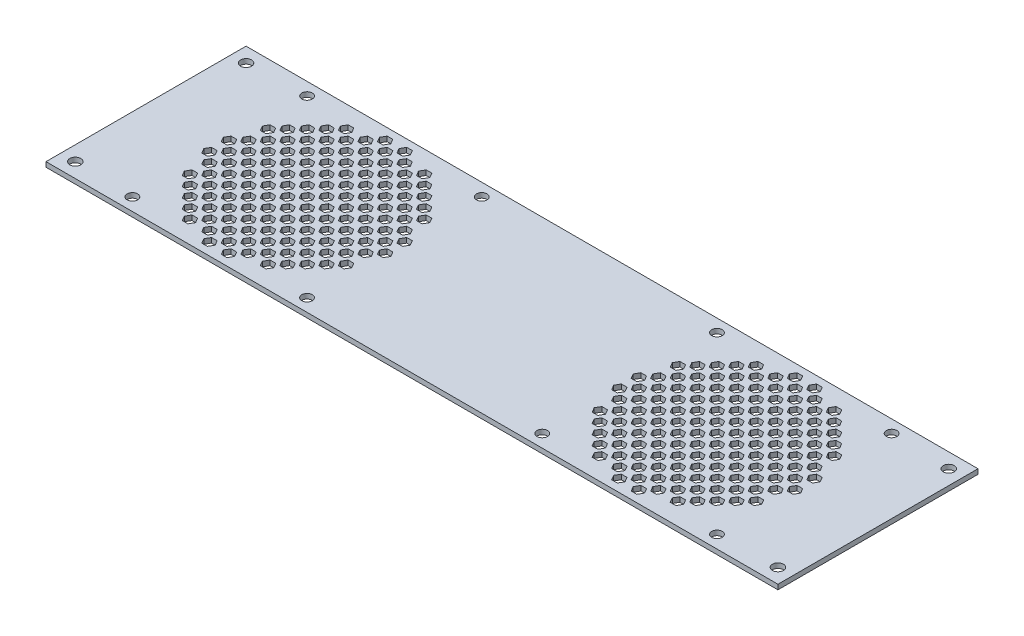
SolidWorks part; units mm, degrees
ref_plane "Front Plane" through (0, 0, 0) normal (0, 0, 1) x (1, 0, 0)
ref_plane "Top Plane" through (0, 0, 0) normal (0, 1, 0) x (1, 0, 0)
ref_plane "Right Plane" through (0, 0, 0) normal (1, 0, 0) x (0, 0, -1)
sketch "Sketch1" plane through (0, 0, 0) normal (0, 1, 0) x (1, 0, 0)
  line L1 (0, 0) -> (300, 0)
  line L2 (0, 0) -> (0, 82)
  line L3 (0, 82) -> (300, 82)
  line L4 (300, 0) -> (300, 82)
  dimension "D1" = 82
  dimension "D2" = 300
extrude "Boss-Extrude1" add sketch "Sketch1" along normal blind 2
hole_wizard "M4 Clearance Hole1" positions "Sketch2" profile "Sketch3" hole size "M4" standard "DIN" end condition up to next
sketch "Sketch2" plane through (0, 0, 0) normal (0, -1, 0) x (-1, 0, 0)
  line L0 (-300, 82) -> (0, 82) construction
  line L1 (-300, 0) -> (-300, 82) construction
  line L2 (0, 0) -> (-300, 0) construction
  line L3 (0, 82) -> (0, 0) construction
  point P0 (-294, 76)
  point P2 (-294, 6)
  point P4 (-6, 6)
  point P6 (-6, 76)
  dimension "D1" = 6
  dimension "D2" = 6
  dimension "D3" = 6
  dimension "D4" = 6
sketch "Sketch3" plane through (294, 0, -76) normal (1, 0, 0) x (0, 0, -1)
  line L0 (0, 0) -> (0, 2)
  line L1 (0, 2) -> (2.25, 2)
  line L2 (2.25, 2) -> (2.25, 0)
  line L5 (2.25, 0) -> (0, 0)
  line L11 (0, -6.35) -> (0, 107.95) construction
  dimension "Thru Hole Dia." = 4.5
  dimension "Thru Hole Depth" = 2
sketch "Sketch5" plane through (0, 0, 0) normal (0, -1, 0) x (1, 0, 0)
  line L0 (0, -82) -> (0, 0) construction
  line L1 (67.1547, -39) -> (64.8453, -39)
  line L2 (64.8453, -39) -> (63.6906, -41)
  line L3 (63.6906, -41) -> (64.8453, -43)
  line L4 (64.8453, -43) -> (67.1547, -43)
  line L5 (67.1547, -43) -> (68.3094, -41)
  line L6 (68.3094, -41) -> (67.1547, -39)
  line L7 (75.1547, -39) -> (72.8453, -39)
  line L8 (72.8453, -39) -> (71.6906, -41)
  line L9 (71.6906, -41) -> (72.8453, -43)
  line L10 (72.8453, -43) -> (75.1547, -43)
  line L11 (75.1547, -43) -> (76.3094, -41)
  line L12 (76.3094, -41) -> (75.1547, -39)
  line L13 (83.1547, -39) -> (80.8453, -39)
  line L14 (80.8453, -39) -> (79.6906, -41)
  line L15 (79.6906, -41) -> (80.8453, -43)
  line L16 (80.8453, -43) -> (83.1547, -43)
  line L17 (83.1547, -43) -> (84.3094, -41)
  line L18 (84.3094, -41) -> (83.1547, -39)
  line L19 (91.1547, -39) -> (88.8453, -39)
  line L20 (88.8453, -39) -> (87.6906, -41)
  line L21 (87.6906, -41) -> (88.8453, -43)
  line L22 (88.8453, -43) -> (91.1547, -43)
  line L23 (91.1547, -43) -> (92.3094, -41)
  line L24 (92.3094, -41) -> (91.1547, -39)
  line L25 (99.1547, -39) -> (96.8453, -39)
  line L26 (96.8453, -39) -> (95.6906, -41)
  line L27 (95.6906, -41) -> (96.8453, -43)
  line L28 (96.8453, -43) -> (99.1547, -43)
  line L29 (99.1547, -43) -> (100.3094, -41)
  line L30 (100.3094, -41) -> (99.1547, -39)
  line L31 (75.1547, -31) -> (72.8453, -31)
  line L32 (72.8453, -31) -> (71.6906, -33)
  line L33 (71.6906, -33) -> (72.8453, -35)
  line L34 (72.8453, -35) -> (75.1547, -35)
  line L35 (75.1547, -35) -> (76.3094, -33)
  line L36 (76.3094, -33) -> (75.1547, -31)
  line L37 (83.1547, -31) -> (80.8453, -31)
  line L38 (80.8453, -31) -> (79.6906, -33)
  line L39 (79.6906, -33) -> (80.8453, -35)
  line L40 (80.8453, -35) -> (83.1547, -35)
  line L41 (83.1547, -35) -> (84.3094, -33)
  line L42 (84.3094, -33) -> (83.1547, -31)
  line L43 (91.1547, -31) -> (88.8453, -31)
  line L44 (88.8453, -31) -> (87.6906, -33)
  line L45 (87.6906, -33) -> (88.8453, -35)
  line L46 (88.8453, -35) -> (91.1547, -35)
  line L47 (91.1547, -35) -> (92.3094, -33)
  line L48 (92.3094, -33) -> (91.1547, -31)
  line L49 (99.1547, -31) -> (96.8453, -31)
  line L50 (96.8453, -31) -> (95.6906, -33)
  line L51 (95.6906, -33) -> (96.8453, -35)
  line L52 (96.8453, -35) -> (99.1547, -35)
  line L53 (99.1547, -35) -> (100.3094, -33)
  line L54 (100.3094, -33) -> (99.1547, -31)
  line L55 (75.1547, -23) -> (72.8453, -23)
  line L56 (72.8453, -23) -> (71.6906, -25)
  line L57 (71.6906, -25) -> (72.8453, -27)
  line L58 (72.8453, -27) -> (75.1547, -27)
  line L59 (75.1547, -27) -> (76.3094, -25)
  line L60 (76.3094, -25) -> (75.1547, -23)
  line L61 (83.1547, -23) -> (80.8453, -23)
  line L62 (80.8453, -23) -> (79.6906, -25)
  line L63 (79.6906, -25) -> (80.8453, -27)
  line L64 (80.8453, -27) -> (83.1547, -27)
  line L65 (83.1547, -27) -> (84.3094, -25)
  line L66 (84.3094, -25) -> (83.1547, -23)
  line L67 (91.1547, -23) -> (88.8453, -23)
  line L68 (88.8453, -23) -> (87.6906, -25)
  line L69 (87.6906, -25) -> (88.8453, -27)
  line L70 (88.8453, -27) -> (91.1547, -27)
  line L71 (91.1547, -27) -> (92.3094, -25)
  line L72 (92.3094, -25) -> (91.1547, -23)
  line L73 (99.1547, -23) -> (96.8453, -23)
  line L74 (96.8453, -23) -> (95.6906, -25)
  line L75 (95.6906, -25) -> (96.8453, -27)
  line L76 (96.8453, -27) -> (99.1547, -27)
  line L77 (99.1547, -27) -> (100.3094, -25)
  line L78 (100.3094, -25) -> (99.1547, -23)
  line L79 (75.1547, -15) -> (72.8453, -15)
  line L80 (72.8453, -15) -> (71.6906, -17)
  line L81 (71.6906, -17) -> (72.8453, -19)
  line L82 (72.8453, -19) -> (75.1547, -19)
  line L83 (75.1547, -19) -> (76.3094, -17)
  line L84 (76.3094, -17) -> (75.1547, -15)
  line L85 (83.1547, -15) -> (80.8453, -15)
  line L86 (80.8453, -15) -> (79.6906, -17)
  line L87 (79.6906, -17) -> (80.8453, -19)
  line L88 (80.8453, -19) -> (83.1547, -19)
  line L89 (83.1547, -19) -> (84.3094, -17)
  line L90 (84.3094, -17) -> (83.1547, -15)
  line L91 (91.1547, -15) -> (88.8453, -15)
  line L92 (88.8453, -15) -> (87.6906, -17)
  line L93 (87.6906, -17) -> (88.8453, -19)
  line L94 (88.8453, -19) -> (91.1547, -19)
  line L95 (91.1547, -19) -> (92.3094, -17)
  line L96 (92.3094, -17) -> (91.1547, -15)
  line L103 (75.1547, -7) -> (72.8453, -7)
  line L104 (72.8453, -7) -> (71.6906, -9)
  line L105 (71.6906, -9) -> (72.8453, -11)
  line L106 (72.8453, -11) -> (75.1547, -11)
  line L107 (75.1547, -11) -> (76.3094, -9)
  line L108 (76.3094, -9) -> (75.1547, -7)
  line L109 (83.1547, -7) -> (80.8453, -7)
  line L110 (80.8453, -7) -> (79.6906, -9)
  line L111 (79.6906, -9) -> (80.8453, -11)
  line L112 (80.8453, -11) -> (83.1547, -11)
  line L113 (83.1547, -11) -> (84.3094, -9)
  line L114 (84.3094, -9) -> (83.1547, -7)
  line L127 (67.1547, -31) -> (64.8453, -31)
  line L128 (64.8453, -31) -> (63.6906, -33)
  line L129 (63.6906, -33) -> (64.8453, -35)
  line L130 (64.8453, -35) -> (67.1547, -35)
  line L131 (67.1547, -35) -> (68.3094, -33)
  line L132 (68.3094, -33) -> (67.1547, -31)
  line L133 (67.1547, -23) -> (64.8453, -23)
  line L134 (64.8453, -23) -> (63.6906, -25)
  line L135 (63.6906, -25) -> (64.8453, -27)
  line L136 (64.8453, -27) -> (67.1547, -27)
  line L137 (67.1547, -27) -> (68.3094, -25)
  line L138 (68.3094, -25) -> (67.1547, -23)
  line L139 (67.1547, -15) -> (64.8453, -15)
  line L140 (64.8453, -15) -> (63.6906, -17)
  line L141 (63.6906, -17) -> (64.8453, -19)
  line L142 (64.8453, -19) -> (67.1547, -19)
  line L143 (67.1547, -19) -> (68.3094, -17)
  line L144 (68.3094, -17) -> (67.1547, -15)
  line L145 (67.1547, -7) -> (64.8453, -7)
  line L146 (64.8453, -7) -> (63.6906, -9)
  line L147 (63.6906, -9) -> (64.8453, -11)
  line L148 (64.8453, -11) -> (67.1547, -11)
  line L149 (67.1547, -11) -> (68.3094, -9)
  line L150 (68.3094, -9) -> (67.1547, -7)
  line L151 (91.1547, -7) -> (88.8453, -7) [skipped]
  line L152 (88.8453, -7) -> (87.6906, -9) [skipped]
  line L153 (87.6906, -9) -> (88.8453, -11) [skipped]
  line L154 (88.8453, -11) -> (91.1547, -11) [skipped]
  line L155 (91.1547, -11) -> (92.3094, -9) [skipped]
  line L156 (92.3094, -9) -> (91.1547, -7) [skipped]
  line L157 (99.1547, -7) -> (96.8453, -7) [skipped]
  line L158 (96.8453, -7) -> (95.6906, -9) [skipped]
  line L159 (95.6906, -9) -> (96.8453, -11) [skipped]
  line L160 (96.8453, -11) -> (99.1547, -11) [skipped]
  line L161 (99.1547, -11) -> (100.3094, -9) [skipped]
  line L162 (100.3094, -9) -> (99.1547, -7) [skipped]
  line L163 (99.1547, -15) -> (96.8453, -15) [skipped]
  line L164 (96.8453, -15) -> (95.6906, -17) [skipped]
  line L165 (95.6906, -17) -> (96.8453, -19) [skipped]
  line L166 (96.8453, -19) -> (99.1547, -19) [skipped]
  line L167 (99.1547, -19) -> (100.3094, -17) [skipped]
  line L168 (100.3094, -17) -> (99.1547, -15) [skipped]
  circle A0 centre (66, -41) radius 2 construction
  point P12 (0, -41)
  dimension "D2" = 4
  dimension "D1" = 66
  dimension "D5" = 8
  dimension "D6" = 8
  dimension "D3" = 5
  dimension "D4" = 5
extrude "Cut-Extrude1" cut sketch "Sketch5" against normal up to next (2 mm away)
sketch "Sketch6" plane through (0, 0, 0) normal (0, -1, 0) x (1, 0, 0)
  line L0 (67.1547, -39) -> (64.8453, -39) construction
  line L1 (72.3094, -37) -> (71.1547, -35)
  line L2 (71.1547, -35) -> (68.8453, -35)
  line L3 (68.8453, -35) -> (67.6906, -37)
  line L4 (67.6906, -37) -> (68.8453, -39)
  line L5 (68.8453, -39) -> (71.1547, -39)
  line L6 (71.1547, -39) -> (72.3094, -37)
  line L7 (64.8453, -43) -> (67.1547, -43) construction
  line L9 (80.3094, -37) -> (79.1547, -35)
  line L10 (79.1547, -35) -> (76.8453, -35)
  line L11 (76.8453, -35) -> (75.6906, -37)
  line L12 (75.6906, -37) -> (76.8453, -39)
  line L13 (76.8453, -39) -> (79.1547, -39)
  line L14 (79.1547, -39) -> (80.3094, -37)
  line L15 (88.3094, -37) -> (87.1547, -35)
  line L16 (87.1547, -35) -> (84.8453, -35)
  line L17 (84.8453, -35) -> (83.6906, -37)
  line L18 (83.6906, -37) -> (84.8453, -39)
  line L19 (84.8453, -39) -> (87.1547, -39)
  line L20 (87.1547, -39) -> (88.3094, -37)
  line L21 (96.3094, -37) -> (95.1547, -35)
  line L22 (95.1547, -35) -> (92.8453, -35)
  line L23 (92.8453, -35) -> (91.6906, -37)
  line L24 (91.6906, -37) -> (92.8453, -39)
  line L25 (92.8453, -39) -> (95.1547, -39)
  line L26 (95.1547, -39) -> (96.3094, -37)
  line L27 (104.3094, -37) -> (103.1547, -35)
  line L28 (103.1547, -35) -> (100.8453, -35)
  line L29 (100.8453, -35) -> (99.6906, -37)
  line L30 (99.6906, -37) -> (100.8453, -39)
  line L31 (100.8453, -39) -> (103.1547, -39)
  line L32 (103.1547, -39) -> (104.3094, -37)
  line L33 (80.3094, -29) -> (79.1547, -27)
  line L34 (79.1547, -27) -> (76.8453, -27)
  line L35 (76.8453, -27) -> (75.6906, -29)
  line L36 (75.6906, -29) -> (76.8453, -31)
  line L37 (76.8453, -31) -> (79.1547, -31)
  line L38 (79.1547, -31) -> (80.3094, -29)
  line L39 (88.3094, -29) -> (87.1547, -27)
  line L40 (87.1547, -27) -> (84.8453, -27)
  line L41 (84.8453, -27) -> (83.6906, -29)
  line L42 (83.6906, -29) -> (84.8453, -31)
  line L43 (84.8453, -31) -> (87.1547, -31)
  line L44 (87.1547, -31) -> (88.3094, -29)
  line L45 (96.3094, -29) -> (95.1547, -27)
  line L46 (95.1547, -27) -> (92.8453, -27)
  line L47 (92.8453, -27) -> (91.6906, -29)
  line L48 (91.6906, -29) -> (92.8453, -31)
  line L49 (92.8453, -31) -> (95.1547, -31)
  line L50 (95.1547, -31) -> (96.3094, -29)
  line L57 (80.3094, -21) -> (79.1547, -19)
  line L58 (79.1547, -19) -> (76.8453, -19)
  line L59 (76.8453, -19) -> (75.6906, -21)
  line L60 (75.6906, -21) -> (76.8453, -23)
  line L61 (76.8453, -23) -> (79.1547, -23)
  line L62 (79.1547, -23) -> (80.3094, -21)
  line L63 (88.3094, -21) -> (87.1547, -19)
  line L64 (87.1547, -19) -> (84.8453, -19)
  line L65 (84.8453, -19) -> (83.6906, -21)
  line L66 (83.6906, -21) -> (84.8453, -23)
  line L67 (84.8453, -23) -> (87.1547, -23)
  line L68 (87.1547, -23) -> (88.3094, -21)
  line L69 (96.3094, -21) -> (95.1547, -19)
  line L70 (95.1547, -19) -> (92.8453, -19)
  line L71 (92.8453, -19) -> (91.6906, -21)
  line L72 (91.6906, -21) -> (92.8453, -23)
  line L73 (92.8453, -23) -> (95.1547, -23)
  line L74 (95.1547, -23) -> (96.3094, -21)
  line L81 (80.3094, -13) -> (79.1547, -11)
  line L82 (79.1547, -11) -> (76.8453, -11)
  line L83 (76.8453, -11) -> (75.6906, -13)
  line L84 (75.6906, -13) -> (76.8453, -15)
  line L85 (76.8453, -15) -> (79.1547, -15)
  line L86 (79.1547, -15) -> (80.3094, -13)
  line L87 (88.3094, -13) -> (87.1547, -11)
  line L88 (87.1547, -11) -> (84.8453, -11)
  line L89 (84.8453, -11) -> (83.6906, -13)
  line L90 (83.6906, -13) -> (84.8453, -15)
  line L91 (84.8453, -15) -> (87.1547, -15)
  line L92 (87.1547, -15) -> (88.3094, -13)
  line L129 (72.3094, -29) -> (71.1547, -27)
  line L130 (71.1547, -27) -> (68.8453, -27)
  line L131 (68.8453, -27) -> (67.6906, -29)
  line L132 (67.6906, -29) -> (68.8453, -31)
  line L133 (68.8453, -31) -> (71.1547, -31)
  line L134 (71.1547, -31) -> (72.3094, -29)
  line L135 (72.3094, -21) -> (71.1547, -19)
  line L136 (71.1547, -19) -> (68.8453, -19)
  line L137 (68.8453, -19) -> (67.6906, -21)
  line L138 (67.6906, -21) -> (68.8453, -23)
  line L139 (68.8453, -23) -> (71.1547, -23)
  line L140 (71.1547, -23) -> (72.3094, -21)
  line L141 (72.3094, -13) -> (71.1547, -11)
  line L142 (71.1547, -11) -> (68.8453, -11)
  line L143 (68.8453, -11) -> (67.6906, -13)
  line L144 (67.6906, -13) -> (68.8453, -15)
  line L145 (68.8453, -15) -> (71.1547, -15)
  line L146 (71.1547, -15) -> (72.3094, -13)
  line L147 (72.3094, -5) -> (71.1547, -3)
  line L148 (71.1547, -3) -> (68.8453, -3)
  line L149 (68.8453, -3) -> (67.6906, -5)
  line L150 (67.6906, -5) -> (68.8453, -7)
  line L151 (68.8453, -7) -> (71.1547, -7)
  line L152 (71.1547, -7) -> (72.3094, -5)
  line L153 (104.3094, -5) -> (103.1547, -3) [skipped]
  line L154 (103.1547, -3) -> (100.8453, -3) [skipped]
  line L155 (100.8453, -3) -> (99.6906, -5) [skipped]
  line L156 (99.6906, -5) -> (100.8453, -7) [skipped]
  line L157 (100.8453, -7) -> (103.1547, -7) [skipped]
  line L158 (103.1547, -7) -> (104.3094, -5) [skipped]
  line L159 (96.3094, -5) -> (95.1547, -3) [skipped]
  line L160 (95.1547, -3) -> (92.8453, -3) [skipped]
  line L161 (92.8453, -3) -> (91.6906, -5) [skipped]
  line L162 (91.6906, -5) -> (92.8453, -7) [skipped]
  line L163 (92.8453, -7) -> (95.1547, -7) [skipped]
  line L164 (95.1547, -7) -> (96.3094, -5) [skipped]
  line L165 (88.3094, -5) -> (87.1547, -3) [skipped]
  line L166 (87.1547, -3) -> (84.8453, -3) [skipped]
  line L167 (84.8453, -3) -> (83.6906, -5) [skipped]
  line L168 (83.6906, -5) -> (84.8453, -7) [skipped]
  line L169 (84.8453, -7) -> (87.1547, -7) [skipped]
  line L170 (87.1547, -7) -> (88.3094, -5) [skipped]
  line L171 (80.3094, -5) -> (79.1547, -3) [skipped]
  line L172 (79.1547, -3) -> (76.8453, -3) [skipped]
  line L173 (76.8453, -3) -> (75.6906, -5) [skipped]
  line L174 (75.6906, -5) -> (76.8453, -7) [skipped]
  line L175 (76.8453, -7) -> (79.1547, -7) [skipped]
  line L176 (79.1547, -7) -> (80.3094, -5) [skipped]
  line L177 (104.3094, -13) -> (103.1547, -11) [skipped]
  line L178 (103.1547, -11) -> (100.8453, -11) [skipped]
  line L179 (100.8453, -11) -> (99.6906, -13) [skipped]
  line L180 (99.6906, -13) -> (100.8453, -15) [skipped]
  line L181 (100.8453, -15) -> (103.1547, -15) [skipped]
  line L182 (103.1547, -15) -> (104.3094, -13) [skipped]
  line L183 (104.3094, -21) -> (103.1547, -19) [skipped]
  line L184 (103.1547, -19) -> (100.8453, -19) [skipped]
  line L185 (100.8453, -19) -> (99.6906, -21) [skipped]
  line L186 (99.6906, -21) -> (100.8453, -23) [skipped]
  line L187 (100.8453, -23) -> (103.1547, -23) [skipped]
  line L188 (103.1547, -23) -> (104.3094, -21) [skipped]
  line L189 (104.3094, -29) -> (103.1547, -27) [skipped]
  line L190 (103.1547, -27) -> (100.8453, -27) [skipped]
  line L191 (100.8453, -27) -> (99.6906, -29) [skipped]
  line L192 (99.6906, -29) -> (100.8453, -31) [skipped]
  line L193 (100.8453, -31) -> (103.1547, -31) [skipped]
  line L194 (103.1547, -31) -> (104.3094, -29) [skipped]
  line L195 (96.3094, -13) -> (95.1547, -11) [skipped]
  line L196 (95.1547, -11) -> (92.8453, -11) [skipped]
  line L197 (92.8453, -11) -> (91.6906, -13) [skipped]
  line L198 (91.6906, -13) -> (92.8453, -15) [skipped]
  line L199 (92.8453, -15) -> (95.1547, -15) [skipped]
  line L200 (95.1547, -15) -> (96.3094, -13) [skipped]
  circle A0 centre (70, -37) radius 2 construction
  dimension "D1" = 4
  dimension "D2" = 4
  dimension "D5" = 8
  dimension "D6" = 8
  dimension "D3" = 5
  dimension "D4" = 5
extrude "Cut-Extrude2" cut sketch "Sketch6" against normal up to next (2 mm away)
ref_plane "Plane1" through (66, 0, 0) normal (-1, 0, 0) x (0, 0, 1)
ref_plane "Plane2" through (0, 0, -41) normal (0, 0, 1) x (1, 0, 0)
mirror "Mirror1" about plane through (66, 0, 0) normal (-1, 0, 0) of "Cut-Extrude2", "Cut-Extrude1"
mirror "Mirror2" about plane through (0, 0, -41) normal (0, 0, 1) of "Mirror1", "Cut-Extrude1", "Cut-Extrude2"
ref_plane "Plane3" through (150, 0, 0) normal (-1, 0, 0) x (0, 0, 1)
mirror "Mirror3" about plane through (150, 0, 0) normal (-1, 0, 0) of "Mirror2", "Cut-Extrude1", "Cut-Extrude2", "Mirror1"
hole_wizard "M4 Clearance Hole2" positions "Sketch7" profile "Sketch8" hole size "M4" standard "DIN"
sketch "Sketch7" plane through (0, 0, 0) normal (0, -1, 0) x (-1, 0, 0)
  line L1 (-269.8, 5.2) -> (-198.2, 5.2) construction
  line L2 (-269.8, 5.2) -> (-269.8, 76.8) construction
  line L3 (-269.8, 76.8) -> (-198.2, 76.8) construction
  line L4 (-198.2, 5.2) -> (-198.2, 76.8) construction
  line L5 (-269.8, 5.2) -> (-198.2, 76.8) construction
  line L6 (-269.8, 76.8) -> (-198.2, 5.2) construction
  line L7 (-235.1547, 43) -> (-232.8453, 43) construction
  line L9 (-101.8, 5.2) -> (-30.2, 5.2) construction
  line L10 (-101.8, 5.2) -> (-101.8, 76.8) construction
  line L11 (-101.8, 76.8) -> (-30.2, 76.8) construction
  line L12 (-30.2, 5.2) -> (-30.2, 76.8) construction
  line L13 (-101.8, 5.2) -> (-30.2, 76.8) construction
  line L14 (-101.8, 76.8) -> (-30.2, 5.2) construction
  line L15 (-64.8453, 43) -> (-67.1547, 43) construction
  point P2 (-198.2, 76.8)
  point P103 (-269.8, 5.2)
  point P104 (-269.8, 76.8)
  point P105 (-198.2, 5.2)
  point P108 (-234, 41)
  point P111 (-234, 43)
  point P124 (-30.2, 76.8)
  point P179 (-101.8, 5.2)
  point P180 (-101.8, 76.8)
  point P181 (-30.2, 5.2)
  point P185 (-66, 41)
  point P188 (-66, 43)
  dimension "D1" = 71.6
sketch "Sketch8" plane through (198.2, 0, -76.8) normal (1, 0, 0) x (0, 0, -1)
  line L0 (0, 0) -> (0, 2)
  line L1 (0, 2) -> (2.15, 2)
  line L2 (2.15, 2) -> (2.15, 0)
  line L5 (2.15, 0) -> (0, 0)
  line L11 (0, -6.35) -> (0, 107.95) construction
  dimension "Thru Hole Dia." = 4.3
  dimension "Thru Hole Depth" = 2
